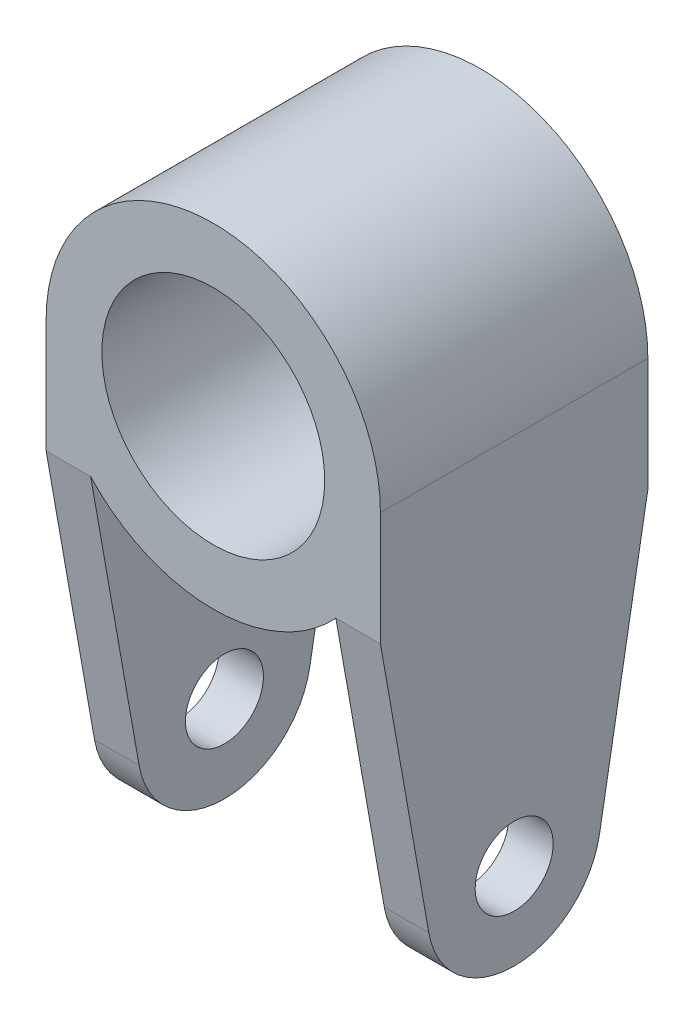
SolidWorks part; units mm, degrees
ref_plane "Front Plane" through (0, 0, 0) normal (0, 0, 1) x (1, 0, 0)
ref_plane "Top Plane" through (0, 0, 0) normal (0, 1, 0) x (1, 0, 0)
ref_plane "Right Plane" through (0, 0, 0) normal (1, 0, 0) x (0, 0, -1)
sketch "Sketch2" plane through (0, 0, 0) normal (0, 0, 1) x (1, 0, 0)
  line L0 (0, -15) -> (-22.6713, -15) construction
  line L1 (-15, 0) -> (-15, -15)
  line L2 (15, 0) -> (15, -22)
  line L3 (-15, -15) -> (-15, -42)
  line L4 (15, -22) -> (15, -42)
  line L5 (-15, -42) -> (-11, -42)
  line L6 (-11, -42) -> (-11, -10.198)
  line L7 (15, -42) -> (11, -42)
  line L8 (11, -42) -> (11, -10.198)
  circle A0 centre (0, 0) radius 10
  arc A1 (-11, -10.198) -> (11, -10.198) centre (0, 0) ccw
  circle A2 centre (0, 0) radius 15 construction
  arc A3 (15, 0) -> (-15, 0) centre (0, 0) ccw
  dimension "D1" = 20
  dimension "D3" = 27
  dimension "D4" = 4
  dimension "D5" = 4
  dimension "D6" = 20
  dimension "D7" = 27
  dimension "D2" = 5
extrude "Boss-Extrude1" add sketch "Sketch2" along normal blind 24
sketch "Sketch3" plane through (-15, 0, 0) normal (-1, 0, 0) x (0, 0, 1)
  line L0 (24, -10.198) -> (0, -10.198) construction
  line L1 (24, -10.198) -> (0, -10.198) construction
  line L2 (12, -42) -> (12, -33.4678) construction
  line L3 (24, -42) -> (0, -42) construction
  line L4 (0, -10.198) -> (4.3412, -34.8182)
  line L5 (19.6588, -34.8182) -> (24, -10.198)
  line L6 (4.3412, -34.8182) -> (19.6588, -34.8182) construction
  line L8 (0, -10.198) -> (0, -42)
  line L10 (24, -10.198) -> (24, -42)
  line L11 (24, -42) -> (0, -42)
  circle A0 centre (12, -33.4678) radius 3.5
  arc A1 (4.3412, -34.8182) -> (19.6588, -34.8182) centre (12, -33.4678) ccw
  dimension "D1" = 7
  dimension "D2" = 25
  dimension "D3" = 80
  dimension "D4" = 31.802
extrude "Cut-Extrude1" cut sketch "Sketch3" against normal up to next
sketch "Sketch4" plane through (15, 0, 0) normal (1, 0, 0) x (0, 0, -1)
  line L5 (0, -10.198) -> (-4.3412, -34.8182)
  line L6 (-19.6588, -34.8182) -> (-24, -10.198)
  line L7 (-24, -10.198) -> (-24, -42)
  line L8 (-24, -42) -> (0, -42)
  line L9 (0, -42) -> (0, -10.198)
  line L10 (0, -10.198) -> (-4.3412, -34.8182)
  line L11 (-19.6588, -34.8182) -> (-24, -10.198)
  line L12 (-24, -10.198) -> (-24, -42)
  line L13 (-24, -42) -> (0, -42)
  line L14 (0, -42) -> (0, -10.198)
  circle A1 centre (-12, -33.4678) radius 3.5
  circle A2 centre (-12, -33.4678) radius 3.5
  arc A3 (-19.6588, -34.8182) -> (-4.3412, -34.8182) centre (-12, -33.4678) ccw
  arc A4 (-19.6588, -34.8182) -> (-4.3412, -34.8182) centre (-12, -33.4678) ccw
  dimension "D1" = 0
  dimension "D2" = 0
extrude "Cut-Extrude2" cut sketch "Sketch4" against normal up to next
